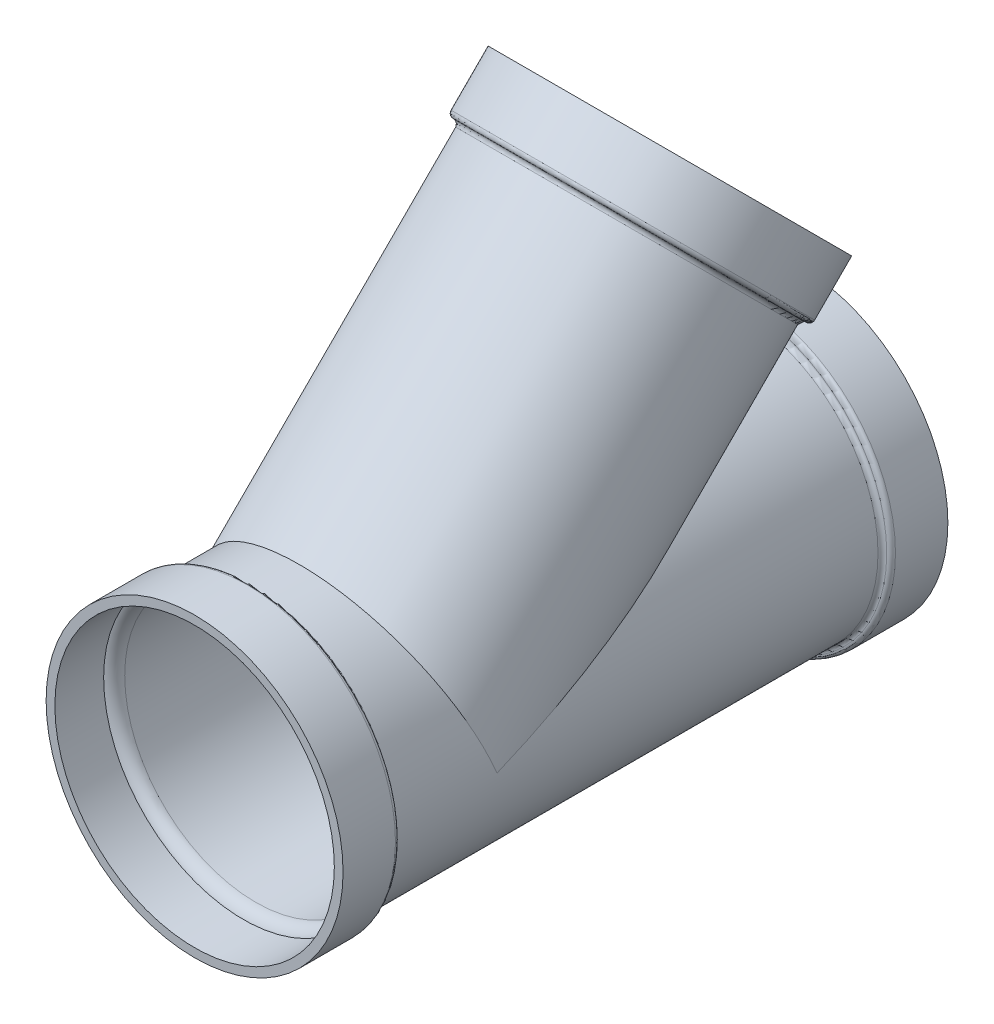
SolidWorks part; units mm, degrees
ref_plane "Front" through (0, 0, 0) normal (0, 0, 1) x (1, 0, 0)
ref_plane "Top" through (0, 0, 0) normal (0, 1, 0) x (1, 0, 0)
ref_plane "Right" through (0, 0, 0) normal (1, 0, 0) x (0, 0, -1)
sketch "Sketch1" plane through (0, 0, 0) normal (1, 0, 0) x (0, 0, -1)
  line L0 (-168.7051, 0) -> (102.8272, 0) construction
  line L1 (-439.7375, 215.9) -> (-363.5375, 215.9)
  line L3 (-350.8375, 203.2) -> (350.8375, 203.2)
  line L5 (363.5375, 215.9) -> (439.7375, 215.9)
  line L6 (439.7375, 215.9) -> (439.7375, 0)
  line L7 (439.7375, 0) -> (-439.7375, 0)
  line L8 (-439.7375, 0) -> (-439.7375, 215.9)
  arc A0 (-357.1875, 209.55) -> (-363.5375, 215.9) centre (-363.5375, 209.55) ccw
  arc A1 (-357.1875, 209.55) -> (-350.8375, 203.2) centre (-350.8375, 209.55) ccw
  arc A2 (350.8375, 203.2) -> (357.1875, 209.55) centre (350.8375, 209.55) ccw
  arc A3 (363.5375, 215.9) -> (357.1875, 209.55) centre (363.5375, 209.55) ccw
  point P5 (0, 203.2)
  dimension "D5" = 6.35
  dimension "D1" = 431.8
  dimension "D2" = 406.4
  dimension "D3" = 879.475
  dimension "D4" = 76.2
revolve "Revolve1" add sketch "Sketch1" angle 360 about L0
sketch "Sketch2" plane through (0, 0, 0) normal (1, 0, 0) x (0, 0, -1)
  line L0 (-203.2, 0) -> (60.6172, 263.8172) construction
  line L1 (251.4255, 454.6255) -> (522.109, 725.309) construction
  line L2 (98.7611, 607.2898) -> (251.4255, 454.6255)
  line L6 (-203.2, 0) -> (-346.8841, 143.6841)
  line L7 (-346.8841, 143.6841) -> (44.8796, 535.4478)
  line L9 (44.8796, 553.4083) -> (98.7611, 607.2898)
  line L10 (439.7375, -215.9) -> (439.7375, 215.9) construction
  line L11 (-203.2, 0) -> (251.4255, 454.6255)
  line L12 (-357.1875, 203.2) -> (-287.3682, 203.2) construction
  line L13 (-357.1875, 209.55) -> (-357.1875, -209.55) construction
  line L14 (350.8375, 203.2) -> (-350.8375, 203.2) construction
  line L16 (287.3682, 203.2) -> (357.1875, 203.2) construction
  line L17 (357.1875, 209.55) -> (357.1875, -209.55) construction
  line L19 (-265.4866, 0) -> (0, 0) construction
  arc A0 (44.8796, 553.4083) -> (44.8796, 544.428) centre (49.3697, 548.9182) ccw
  arc A5 (44.8796, 535.4478) -> (44.8796, 544.428) centre (40.3894, 539.9379) ccw
  dimension "D6" = 6.35
  dimension "D1" = 642.9375
  dimension "D2" = 642.9375
  dimension "D3" = 431.8
  dimension "D4" = 406.4
  dimension "D5" = 76.2
  dimension "D7" = 45
revolve "Revolve2" add sketch "Sketch2" angle 360 about L0
sketch "Sketch4" plane through (0, 0, 0) normal (1, 0, 0) x (0, 0, -1)
  line L5 (-203.2, 0) -> (251.4255, 454.6255)
  line L7 (251.4255, 454.6255) -> (107.7414, 598.3096)
  line L9 (404.0898, 301.9611) -> (98.7611, 607.2898) construction
  line L10 (-328.9236, 143.6841) -> (-203.2, 17.9605)
  line L11 (-203.2, 17.9605) -> (233.465, 454.6255)
  line L12 (233.465, 454.6255) -> (98.7611, 589.3293)
  line L13 (98.7611, 589.3293) -> (57.5796, 548.1478)
  line L14 (53.8598, 526.4675) -> (-328.9236, 143.6841)
  line L18 (107.7414, 598.3096) -> (57.5796, 548.1478)
  line L19 (53.8598, 526.4675) -> (-337.9038, 134.7038)
  line L20 (-203.2, 0) -> (60.6172, 263.8172) construction
  line L21 (-337.9038, 134.7038) -> (-203.2, 0)
  line L22 (-203.2, 0) -> (-287.3682, 203.2) construction
  arc A2 (53.8598, 526.4675) -> (57.5796, 548.1478) centre (40.3894, 539.9379) ccw
  arc A6 (53.8598, 526.4675) -> (57.5796, 548.1478) centre (40.3894, 539.9379) ccw
  dimension "D1" = 12.7
revolve "Cut-Revolve1" cut sketch "Sketch4" angle 360 about L0
sketch "Sketch5" plane through (0, 0, 0) normal (1, 0, 0) x (0, 0, -1)
  line L6 (-439.7375, 0) -> (439.7375, 0)
  line L8 (439.7375, 0) -> (439.7375, 203.2)
  line L9 (-439.7375, 0) -> (-439.7375, 203.2)
  line L12 (350.8375, 190.5) -> (-350.8375, 190.5)
  line L13 (427.0375, 203.2) -> (368.798, 203.2)
  line L14 (427.0375, 12.7) -> (427.0375, 203.2)
  line L15 (-427.0375, 12.7) -> (427.0375, 12.7)
  line L16 (-427.0375, 203.2) -> (-427.0375, 12.7)
  line L17 (-368.798, 203.2) -> (-427.0375, 203.2)
  line L18 (350.8375, 190.5) -> (-350.8375, 190.5)
  line L19 (439.7375, 203.2) -> (368.798, 203.2)
  line L23 (-368.798, 203.2) -> (-439.7375, 203.2)
  arc A8 (350.8375, 190.5) -> (368.798, 203.2) centre (350.8375, 209.55) ccw
  arc A9 (-368.798, 203.2) -> (-350.8375, 190.5) centre (-350.8375, 209.55) ccw
  arc A10 (350.8375, 190.5) -> (368.798, 203.2) centre (350.8375, 209.55) ccw
  arc A11 (-368.798, 203.2) -> (-350.8375, 190.5) centre (-350.8375, 209.55) ccw
  dimension "D1" = 12.7
revolve "Cut-Revolve2" cut sketch "Sketch5" angle 360 about L0
